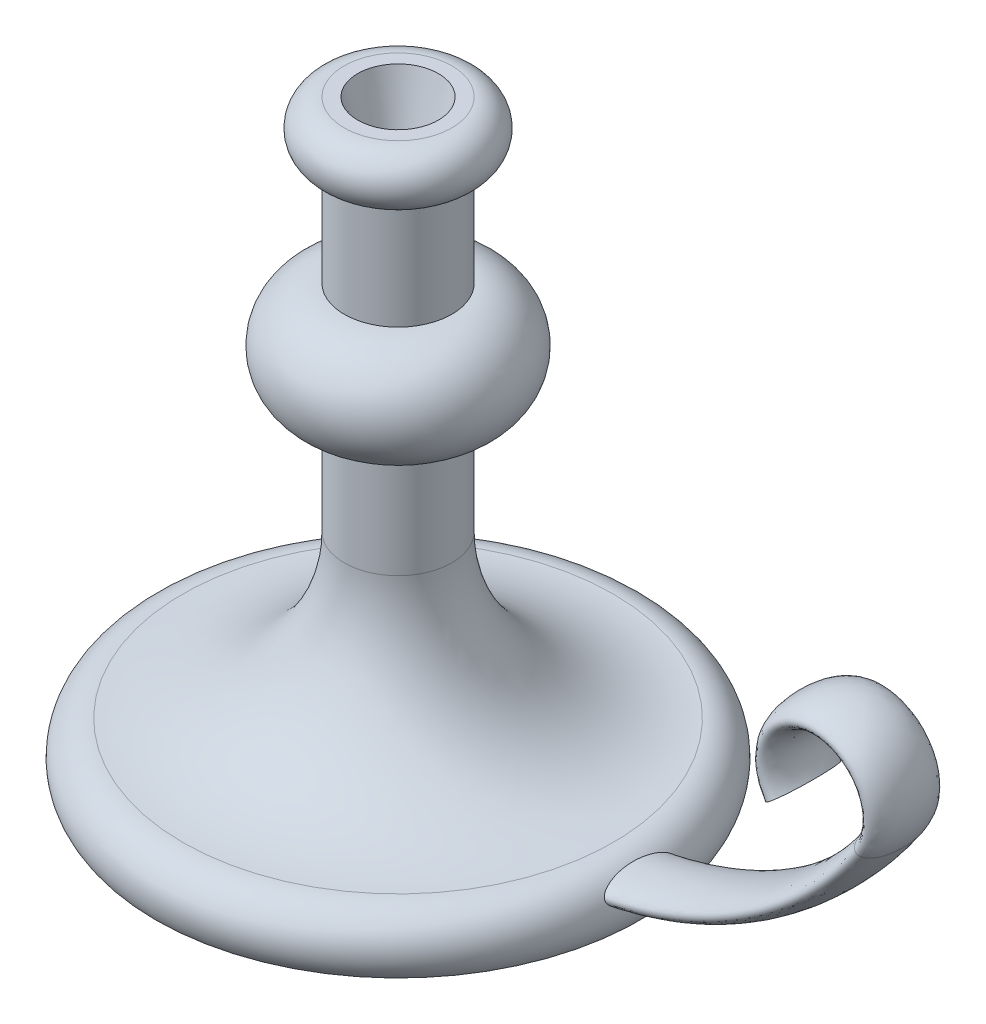
SolidWorks part; units mm, degrees
ref_plane "Front Plane" through (0, 0, 0) normal (0, 0, 1) x (1, 0, 0)
ref_plane "Top Plane" through (0, 0, 0) normal (0, 1, 0) x (1, 0, 0)
ref_plane "Right Plane" through (0, 0, 0) normal (1, 0, 0) x (0, 0, -1)
sketch "Sketch2" plane through (0, 0, 0) normal (0, 0, 1) x (1, 0, 0)
  line L0 (0, 0) -> (0, 220)
  line L1 (0, 0) -> (90, 0)
  line L2 (0, 220) -> (20, 220)
  line L3 (20, 200) -> (20, 160)
  line L4 (20, 120) -> (20, 80)
  arc A0 (20, 220) -> (20, 200) centre (20, 210) cw
  arc A1 (20, 160) -> (20, 120) centre (20, 140) cw
  arc A2 (20, 80) -> (80, 20) centre (80, 80) ccw
  arc A3 (80, 20) -> (90, 0) centre (80, 7.5) cw
  dimension "D4" = 10
  dimension "D5" = 20
  dimension "D7" = 60
  dimension "D8" = 12.5
  dimension "D1" = 220
  dimension "D2" = 90
  dimension "D3" = 20
  dimension "D6" = 40
  dimension "D9" = 80
revolve "Revolve1" add sketch "Sketch2" angle 360 about L0
sketch "Sketch3" plane through (0, 0, 0) normal (0, 0, 1) x (1, 0, 0)
  line L0 (0, 10) -> (60, 10)
  line L1 (0, 227.4356) -> (0, 175.1288) construction
  line L2 (0, 164) -> (0, 92) construction
  line L3 (-90, 0) -> (90, 0) construction
  arc A0 (60, 10) -> (183.5921, 75) centre (60, 160) ccw
  arc A1 (183.5921, 75) -> (150.6342, 75) centre (167.1131, 86.3333) ccw
  point P12 (0, 0)
  point P13 (0, 0)
  dimension "D2" = 150
  dimension "D4" = 20
  dimension "D1" = 60
  dimension "D3" = 65
  dimension "D5" = 10
sketch "Sketch5" plane through (0, 0, 0) normal (1, 0, 0) x (0, 0, -1)
  ellipse E0 centre (0, 10) end of major axis (-13.3333, 10) minor radius 5
  point P1 (0, 0)
  point P7 (0, 0)
  point P8 (0, 0)
  point P10 (0, 0)
  dimension "D1" = 10
  dimension "D2" = 26.6667
sweep "Sweep1" add profiles "Sketch5" path "Sketch3"
sketch "Sketch6" plane through (0, 220, 0) normal (0, 1, 0) x (1, 0, 0)
  circle A0 centre (0, 0) radius 15
  dimension "D1" = 30
extrude "Cut-Extrude1" cut sketch "Sketch6" against normal blind 25 draft 15
